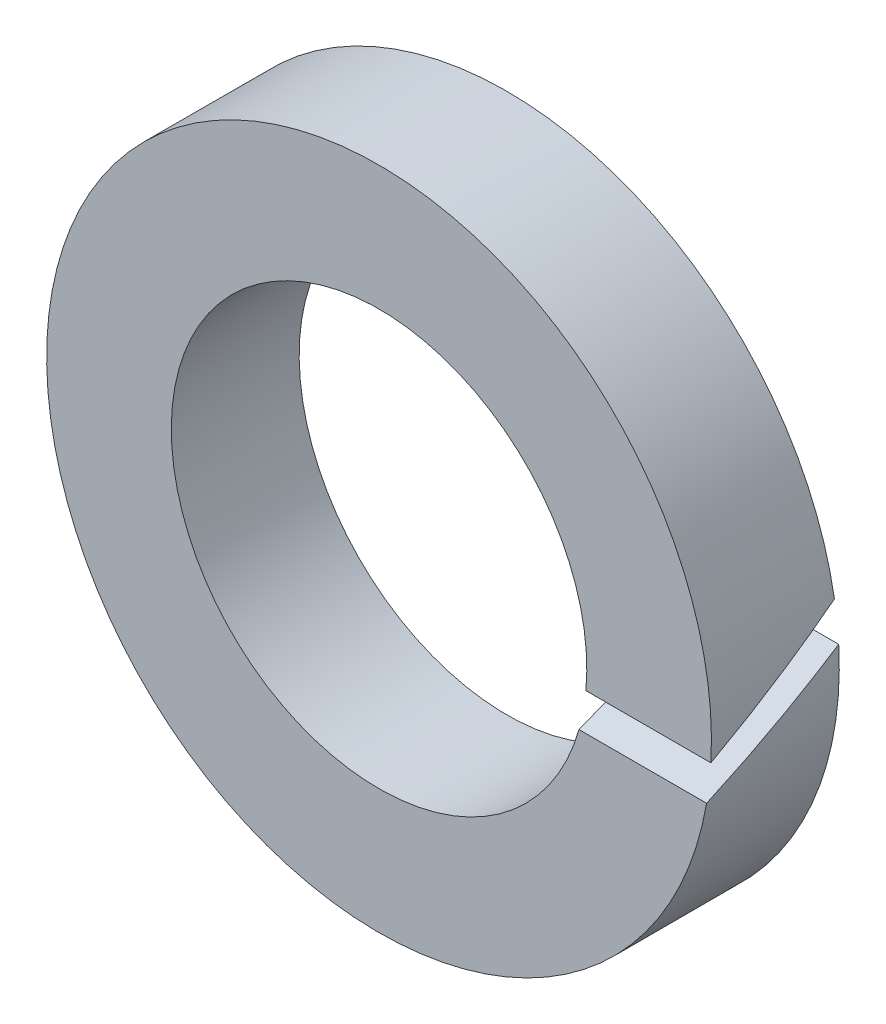
SolidWorks part; units mm, degrees
ref_plane "Plane1" through (0, 0, 0) normal (0, 0, 1) x (1, 0, 0)
ref_plane "Plane2" through (0, 0, 0) normal (0, 1, 0) x (1, 0, 0)
ref_plane "Plane3" through (0, 0, 0) normal (1, 0, 0) x (0, 0, -1)
sketch "Esquisse1" plane through (0, 0, 0) normal (0, 0, 1) x (1, 0, 0)
  circle A0 centre (0, 0) radius 5.2
  circle A1 centre (0, 0) radius 3.25
  dimension "D1" = 10.4
  dimension "D2" = 6.5
extrude "Base-Extrusion" add sketch "Esquisse1" along normal blind 2
sketch "Esquisse2" plane through (0, 0, 0) normal (1, 0, 0) x (0, 0, -1)
  line L0 (-2, 0) -> (0, 0) construction
  line L1 (-2, 0) -> (0, 0) construction
  line L2 (-2, -0.3027) -> (0, 0.8841)
  line L3 (0, -5.2) -> (0, 5.2) construction
  line L4 (-2, 5.2) -> (-2, -5.2) construction
  line L5 (-1, 0) -> (2.0955, 1.8367) construction
  line L6 (-2, -0.8841) -> (0, 0.3027)
  line L7 (0, 0.8841) -> (0, 0.3027)
  line L8 (-2, -0.3027) -> (-2, -0.8841)
  dimension "D1" = 0.5
extrude "Enlèv. mat.-Extru.1" cut sketch "Esquisse2" along normal through all
